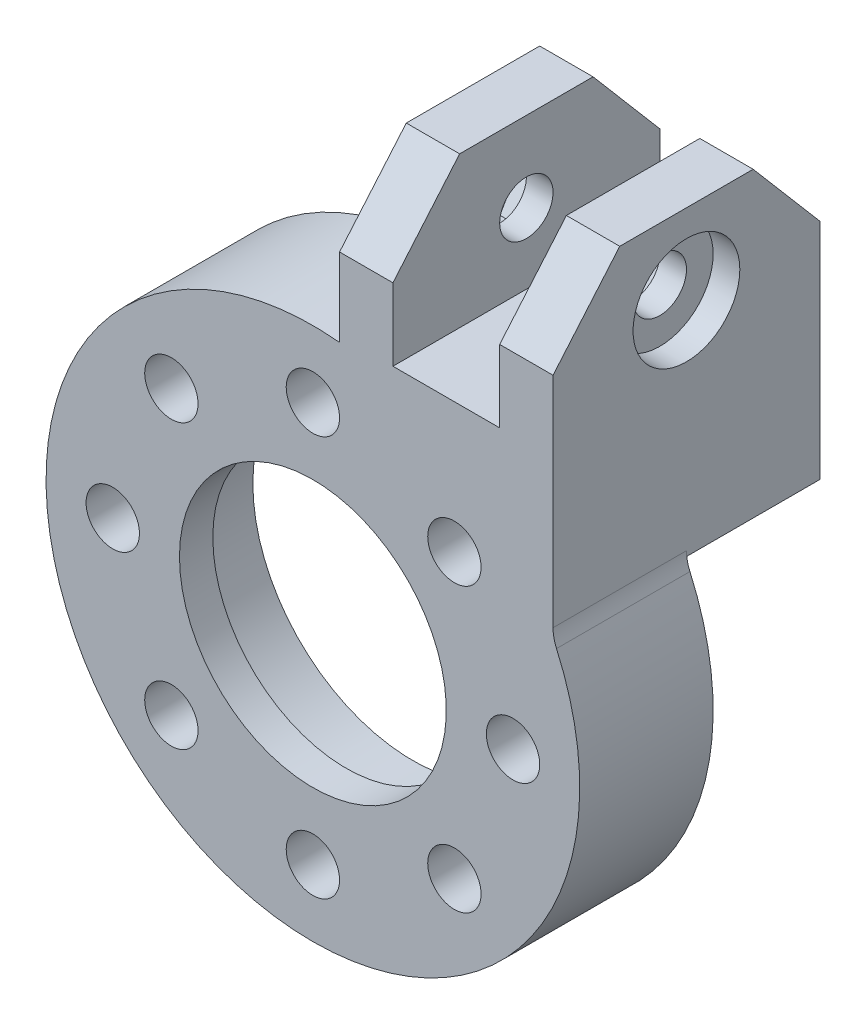
SolidWorks part; units mm, degrees
ref_plane "Front Plane" through (0, 0, 0) normal (0, 0, 1) x (1, 0, 0)
ref_plane "Top Plane" through (0, 0, 0) normal (0, 1, 0) x (1, 0, 0)
ref_plane "Right Plane" through (0, 0, 0) normal (1, 0, 0) x (0, 0, -1)
sketch "Sketch1" plane through (0, 0, 0) normal (0, 0, 1) x (1, 0, 0)
  circle A0 centre (0, 0) radius 20
  circle A1 centre (0, 0) radius 15
  dimension "D1" = 40
  dimension "D2" = 30
extrude "Boss-Extrude1" add sketch "Sketch1" along normal blind 10
sketch "Sketch2" plane through (0, 0, 10) normal (0, 0, 1) x (1, 0, 0)
  line L0 (2, 14.8661) -> (2, 39.8661)
  line L1 (0, 20) -> (0, 15) construction
  line L3 (2, 39.8661) -> (6, 39.8661)
  line L4 (2, 39.8661) -> (2, 14.8661)
  line L5 (2, 14.8661) -> (6, 14.8661)
  line L6 (6, 39.8661) -> (6, 14.8661)
  circle A0 centre (0, 0) radius 20 construction
  circle A1 centre (0, 0) radius 15 construction
  circle M8 centre (0, 0) radius 20
  dimension "D1" = 25
  dimension "D2" = 2
  dimension "D3" = 4
extrude "Boss-Extrude2" add sketch "Sketch2" against normal blind 20 contours L6 L3 L0 M8
sketch "Sketch3" plane through (0, 0, 10) normal (0, 0, 1) x (1, 0, 0)
  line L0 (6, 39.8661) -> (6, 19.0788) construction
  line L1 (14, 40.6404) -> (18, 40.6404)
  line L2 (14, 40.6404) -> (14, 8.7178)
  line L3 (14, 8.7178) -> (18, 8.7178)
  line L4 (18, 40.6404) -> (18, 8.7178)
  arc A0 (2, 19.8997) -> (6, 19.0788) centre (0, 0) ccw construction
  dimension "D1" = 8
  dimension "D2" = 4
extrude "Boss-Extrude4" add sketch "Sketch3" against normal blind 20
sketch "Sketch5" plane through (0, 0, 10) normal (0, 0, 1) x (1, 0, 0)
  line L0 (14, 20.3535) -> (10.604, 16.9575)
  line L1 (14, 40.6404) -> (14, 14.2829) construction
  line L2 (10.604, 16.9575) -> (14, 14.2829)
  line L3 (14, 14.2829) -> (14, 20.3535)
  arc A0 (14, 14.2829) -> (6, 19.0788) centre (0, 0) ccw construction
  dimension "D1" = 45
extrude "Boss-Extrude5" add sketch "Sketch5" against normal blind 20
sketch "Sketch4" plane through (0, 0, 0) normal (0, 0, -1) x (-1, 0, 0)
  circle A0 centre (0, 0) radius 20
extrude "Cut-Extrude1" cut sketch "Sketch4" along normal through all
sketch "Sketch6" plane through (18, 0, 0) normal (1, 0, 0) x (0, 0, -1)
  line L0 (-10, 40.6404) -> (-6, 40.6404)
  line L1 (10, 40.6404) -> (-10, 40.6404) construction
  line L2 (-6, 40.6404) -> (-10, 36.6404)
  line L3 (-10, 8.7178) -> (-10, 40.6404) construction
  line L4 (-10, 36.6404) -> (-10, 40.6404)
  dimension "D1" = 4
  dimension "D2" = 4
extrude "Cut-Extrude2" cut sketch "Sketch6" against normal through all
sketch "Sketch7" plane through (18, 0, 0) normal (1, 0, 0) x (0, 0, -1)
  line L0 (10, 40.6404) -> (6, 40.6404)
  line L1 (10, 40.6404) -> (-6, 40.6404) construction
  line L2 (6, 40.6404) -> (10, 36.6404)
  line L3 (10, 8.7178) -> (10, 40.6404) construction
  line L4 (10, 36.6404) -> (10, 40.6404)
  dimension "D1" = 4
  dimension "D2" = 4
extrude "Cut-Extrude3" cut sketch "Sketch7" against normal through all
sketch "Sketch8" plane through (18, 0, 0) normal (1, 0, 0) x (0, 0, -1)
  line L0 (0, 40.6404) -> (0, 25.6404) construction
  line L1 (6, 40.6404) -> (-6, 40.6404) construction
  circle A0 centre (0, 25.6404) radius 2
  dimension "D2" = 4
  dimension "D1" = 15
extrude "Cut-Extrude4" cut sketch "Sketch8" against normal through all
fillet "Fillet4" radius 3 1 edges at (18, 8.7178, 5)
sketch "Sketch9" plane through (18, 0, 0) normal (1, 0, 0) x (0, 0, -1)
  line L0 (-10, 9.3808) -> (-10, 36.6404) construction
  line L1 (-10, 31.6404) -> (11.0071, 31.6404)
  line L2 (-10, 31.6404) -> (-10, 41.9547)
  line L3 (-10, 41.9547) -> (11.0071, 41.9547)
  line L4 (11.0071, 31.6404) -> (11.0071, 41.9547)
  line L5 (6, 40.6404) -> (-6, 40.6404) construction
  dimension "D1" = 9
extrude "Cut-Extrude5" cut sketch "Sketch9" against normal through all and the other way through all
sketch "Sketch10" plane through (2, 0, 0) normal (-1, 0, 0) x (0, 0, 1)
  line L0 (10, 31.6404) -> (5, 31.6404)
  line L1 (10, 31.6404) -> (-10, 31.6404) construction
  line L2 (5, 31.6404) -> (10, 25.7701)
  line L3 (10, 19.8997) -> (10, 31.6404) construction
  line L4 (10, 25.7701) -> (10, 31.6404)
  dimension "D1" = 5
extrude "Cut-Extrude6" cut sketch "Sketch10" against normal through all
sketch "Sketch11" plane through (2, 0, 0) normal (-1, 0, 0) x (0, 0, 1)
  line L0 (-10, 31.6404) -> (-10, 25.7701)
  line L1 (-10, 19.8997) -> (-10, 31.6404) construction
  line L2 (-10, 25.7701) -> (-5, 31.6404)
  line L3 (5, 31.6404) -> (-10, 31.6404) construction
  line L4 (-5, 31.6404) -> (-10, 31.6404)
  dimension "D1" = 5
extrude "Cut-Extrude7" cut sketch "Sketch11" against normal through all
sketch "Sketch12" plane through (18, 0, 0) normal (1, 0, 0) x (0, 0, -1)
  circle A0 centre (0, 25.6404) radius 4
  dimension "D1" = 8
extrude "Cut-Extrude8" cut sketch "Sketch12" against normal blind 2
sketch "Sketch13" plane through (2, 0, 0) normal (-1, 0, 0) x (0, 0, 1)
  line L1 (4.0415, 25.6404) -> (2.0207, 29.1404)
  line L2 (2.0207, 29.1404) -> (-2.0207, 29.1404)
  line L3 (-2.0207, 29.1404) -> (-4.0415, 25.6404)
  line L4 (-4.0415, 25.6404) -> (-2.0207, 22.1404)
  line L5 (-2.0207, 22.1404) -> (2.0207, 22.1404)
  line L6 (2.0207, 22.1404) -> (4.0415, 25.6404)
  circle A0 centre (0, 25.6404) radius 3.5 construction
  dimension "D1" = 7
extrude "Cut-Extrude9" cut sketch "Sketch13" against normal blind 2
sketch "Sketch16" plane through (0, 0, 10) normal (0, 0, 1) x (1, 0, 0)
  line L0 (14, 20.3535) -> (6, 20.3535)
  line L1 (6, 25.7701) -> (6, 19.0788) construction
  line L2 (6, 20.3535) -> (6, 19.0788)
  line L3 (14, 20.3535) -> (10.604, 16.9575)
  arc A0 (10.604, 16.9575) -> (6, 19.0788) centre (0, 0) ccw
extrude "Boss-Extrude7" add sketch "Sketch16" against normal blind 20
sketch "Sketch19" plane through (0, 0, 0) normal (0, 0, -1) x (-1, 0, 0)
  circle A0 centre (0, 0) radius 20.125
  dimension "D1" = 40.25
extrude "Cut-Extrude11" cut sketch "Sketch19" along normal through all
sketch "Sketch20" plane through (0, 0, 10) normal (0, 0, 1) x (1, 0, 0)
  circle A0 centre (0, 0) radius 12
  circle A1 centre (0, 0) radius 15
  dimension "D1" = 24
extrude "Boss-Extrude8" add sketch "Sketch20" against normal blind 10
sketch "Sketch21" plane through (0, 0, 10) normal (0, 0, 1) x (1, 0, 0)
  circle A0 centre (0, 0) radius 12
extrude "Boss-Extrude9" add sketch "Sketch21" against normal blind 2.5
sketch "Sketch22" plane through (0, 0, 7.5) normal (0, 0, -1) x (-1, 0, 0)
  circle A0 centre (0, 0) radius 10
  dimension "D1" = 20
extrude "Cut-Extrude12" cut sketch "Sketch22" against normal blind 2.5
sketch "Sketch23" plane through (0, 0, 0) normal (0, 0, -1) x (-1, 0, 0)
  circle A0 centre (0, 0) radius 17.5
  dimension "D1" = 35
extrude "Cut-Extrude13" cut sketch "Sketch23" against normal blind 2.5
sketch "Sketch24" plane through (0, 0, 2.5) normal (0, 0, -1) x (-1, 0, 0)
  circle A0 centre (0, 0) radius 15
  circle A1 centre (0, 15) radius 2
  circle A2 centre (10.6066, 10.6066) radius 2
  circle A3 centre (15, 0) radius 2
  circle A4 centre (10.6066, -10.6066) radius 2
  circle A5 centre (0, -15) radius 2
  circle A6 centre (-10.6066, -10.6066) radius 2
  circle A7 centre (-15, 0) radius 2
  circle A8 centre (-10.6066, 10.6066) radius 2
  point P22 (0, 0)
  dimension "D1" = 30
  dimension "D2" = 4
  dimension "D3" = 8
extrude "Cut-Extrude14" cut sketch "Sketch24" against normal through all contours A8 | A1 | A2 | A3 | A4 | A5 | A6 | A7
